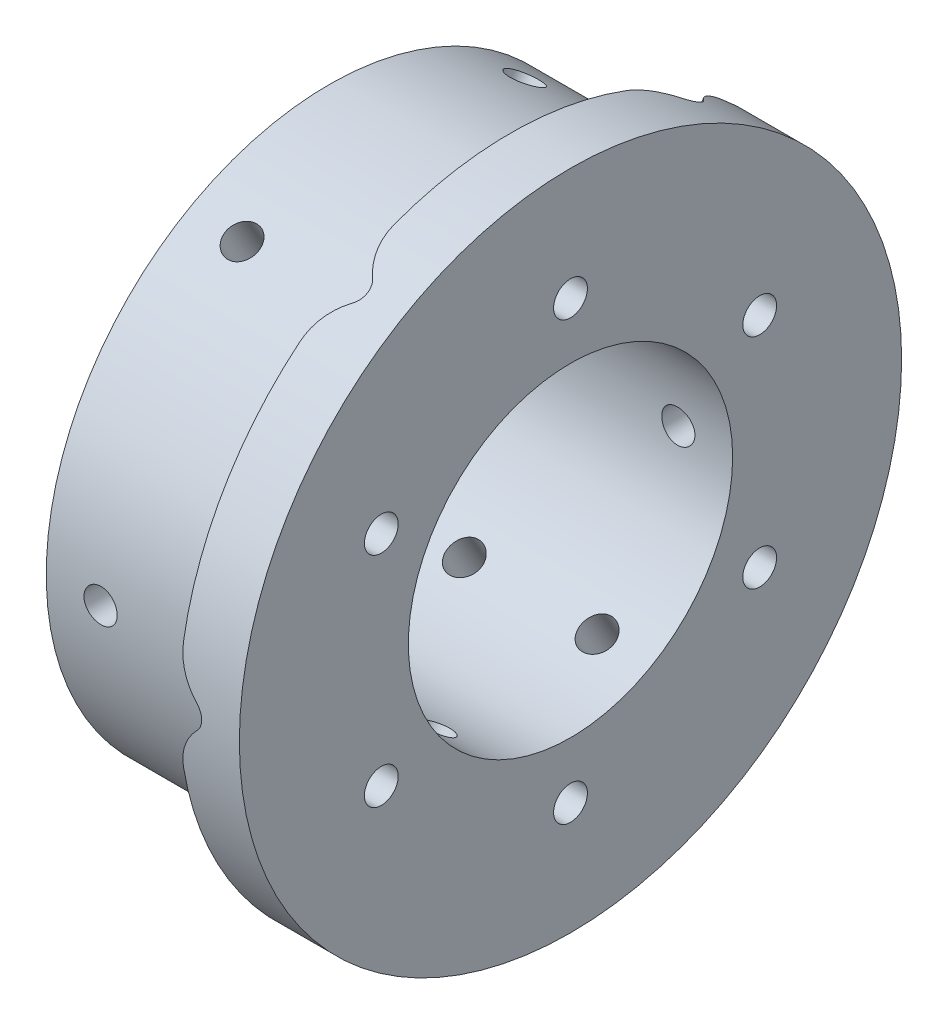
SolidWorks part; units mm, degrees
ref_plane "Front Plane" through (0, 0, 0) normal (0, 0, 1) x (1, 0, 0)
ref_plane "Top Plane" through (0, 0, 0) normal (0, 1, 0) x (1, 0, 0)
ref_plane "Right Plane" through (0, 0, 0) normal (1, 0, 0) x (0, 0, -1)
sketch "Sketch1" plane through (0, 0, 0) normal (1, 0, 0) x (0, 0, -1)
  circle A0 centre (0, 0) radius 13.435
  circle A1 centre (0, 0) radius 23.435
  circle A2 centre (0, 0) radius 18.1 construction
  circle A3 centre (0, 18.1) radius 1.4
  circle A4 centre (15.6751, 9.05) radius 1.4
  circle A5 centre (15.6751, -9.05) radius 1.4
  circle A6 centre (0, -18.1) radius 1.4
  circle A7 centre (-15.6751, -9.05) radius 1.4
  circle A8 centre (-15.6751, 9.05) radius 1.4
  point P20 (0, 0)
  dimension "D1" = 10
  dimension "D2" = 26.87
  dimension "D3" = 36.2
  dimension "D4" = 2.8
  dimension "D5" = 6
extrude "Boss-Extrude1" add sketch "Sketch1" along normal mid plane 20
sketch "Sketch4" plane through (10, 0, 0) normal (1, 0, 0) x (0, 0, -1)
  circle A0 centre (0, 0) radius 23.435 construction
  circle A1 centre (0, 0) radius 23.435
  circle A2 centre (0, 0) radius 27.435
  dimension "D1" = 4
extrude "Boss-Extrude2" add sketch "Sketch4" against normal blind 5
sketch "Sketch3" plane through (0, 0, 0) normal (0, 0, 1) x (1, 0, 0)
  circle A0 centre (5.5, 0) radius 1.375
  dimension "D1" = 5.5
  dimension "D2" = 2.75
extrude "Cut-Extrude1" cut sketch "Sketch3" against normal through all
pattern_circular "CirPattern1" count 6 over 360 about axis through (10, 0, 0) along (-1, 0, 0) of "Cut-Extrude1"
pattern_linear "LPattern1" count 2 spacing 11 along (-1, 0, 0) of "CirPattern1", "Cut-Extrude1"
fillet "Fillet1" radius 5 18 edges at (5, -1.2809, -25.4025) (5, 1.2809, -25.4025) (6.875, 0, -27.435) (5, -21.3588, 13.8105) (5, -22.6397, 11.592) (5, 1.2809, 25.4025) (5, -1.2809, 25.4025) (5, 22.6397, 11.592) (5, 21.3588, 13.8105) (5, -21.3588, -13.8105) (5, -22.6397, -11.592) (5, 21.3588, -13.8105) (5, 22.6397, -11.592) (4.1587, 23.6067, -13.9787) (4.1251, -23.7534, -13.728) (4.1587, 23.9092, 13.4547) (6.8672, -0.1462, 27.4346) (4.1587, -23.6067, 13.9787)
